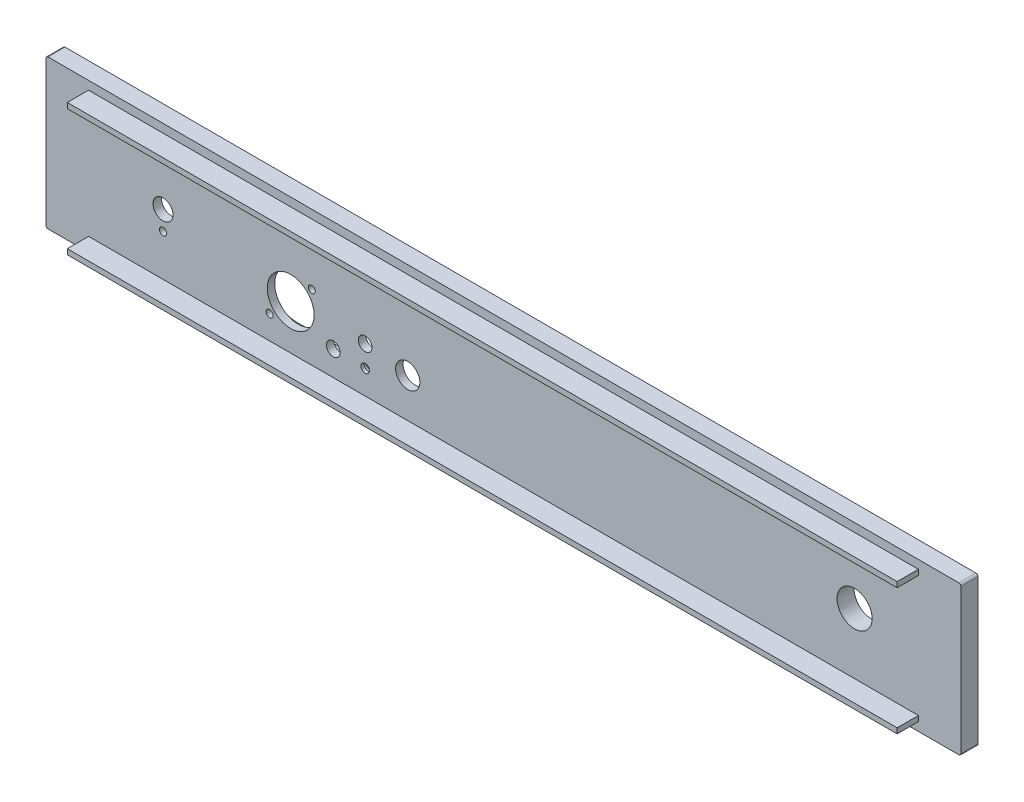
SolidWorks part; units mm, degrees
ref_plane "前基準面" through (0, 0, 0) normal (0, 0, 1) x (1, 0, 0)
ref_plane "上基準面" through (0, 0, 0) normal (0, 1, 0) x (1, 0, 0)
ref_plane "右基準面" through (0, 0, 0) normal (1, 0, 0) x (0, 0, -1)
sketch "草圖1" plane through (0, 0, 0) normal (0, 0, 1) x (1, 0, 0)
  line L1 (-215, -35) -> (215, -35)
  line L2 (-215, -35) -> (-215, 35)
  line L3 (-215, 35) -> (215, 35)
  line L4 (215, -35) -> (215, 35)
  line L5 (-215, -35) -> (215, 35) construction
  line L6 (-215, 35) -> (215, -35) construction
  point P0 (0, 0)
  dimension "D1" = 70
  dimension "D2" = 430
extrude "填料-伸長1" add sketch "草圖1" along normal blind 8
fillet "圓角1" radius 1 4 edges at (-215, 35, 4) (-215, -35, 4) (215, -35, 4) (215, 35, 4)
sketch "草圖2" plane through (0, 0, 8) normal (0, 0, 1) x (1, 0, 0)
  line L0 (214, 35) -> (-214, 35) construction
  line L1 (-195, 31) -> (195, 31)
  line L2 (-195, 31) -> (-195, 28.5)
  line L3 (-195, 28.5) -> (195, 28.5)
  line L4 (195, 31) -> (195, 28.5)
  line L5 (195, -28.5) -> (-195, -28.5)
  line L6 (195, -28.5) -> (195, -31)
  line L7 (195, -31) -> (-195, -31)
  line L8 (-195, -28.5) -> (-195, -31)
  line L9 (-215, 34) -> (-215, -34) construction
  line L11 (215, -34) -> (215, 34) construction
  dimension "D1" = 4
  dimension "D2" = 62
  dimension "D3" = 2.5
  dimension "D4" = 2.5
  dimension "D5" = 20
  dimension "D6" = 20
  dimension "D7" = 20
extrude "填料-伸長2" add sketch "草圖2" along normal blind 10
sketch "草圖3" plane through (0, 0, 0) normal (0, 0, -1) x (-1, 0, 0)
  line L0 (215, 0) -> (-215, 0)
  line L1 (215, 34) -> (215, -34) construction
  line L2 (-215, -34) -> (-215, 34) construction
  line L3 (115, -20) -> (35, -20)
  line L5 (214, -35) -> (-214, -35) construction
  circle A0 centre (-180.2944, 0) radius 8.6085
  circle A1 centre (100, -7.5) radius 11
  circle A2 centre (90.1, 2.4) radius 1.65
  circle A3 centre (109.9, -17.4) radius 1.65
  circle A4 centre (80, -16.75) radius 3.25
  circle A5 centre (65, -17.2) radius 2
  circle A6 centre (45, -10.11) radius 5.7
  circle A7 centre (160, 0) radius 4.7
  circle A8 centre (160, -9) radius 1.7
  circle A9 centre (65, -7.2) radius 3.2
  dimension "D2" = 4
  dimension "D4" = 22
  dimension "D9" = 3.3
  dimension "D10" = 3.3
  dimension "D15" = 6.5
  dimension "D16" = 11.4
  dimension "D22" = 9.4
  dimension "D24" = 3.4
  dimension "D26" = 6.4
  dimension "D1" = 12.5
  dimension "D3" = 2.8
  dimension "D5" = 19.8
  dimension "D6" = 19.8
  dimension "D7" = 9.9
  dimension "D8" = 9.9
  dimension "D11" = 20
  dimension "D12" = 15
  dimension "D13" = 20
  dimension "D14" = 3.25
  dimension "D17" = 9.89
  dimension "D18" = 10
  dimension "D19" = 15
  dimension "D20" = 100
  dimension "D21" = 15
  dimension "D23" = 9
  dimension "D25" = 60
  dimension "D27" = 20
  dimension "D28" = 10
extrude "除料-伸長1" cut sketch "草圖3" against normal through all contours A2 | L0 A1 | L0 A1 | A3 | A4 | A6 | A7 | A8 | L0 A7 | A5 | A9
sketch "草圖4" plane through (0, 0, 0) normal (0, 0, -1) x (-1, 0, 0)
  line L0 (45, -7.5) -> (105, -7.5) construction
  line L1 (45, 7.5) -> (105, 7.5)
  line L2 (45, -22.5) -> (105, -22.5)
  line L3 (214, -35) -> (-214, -35) construction
  line L4 (215, 34) -> (215, -34) construction
  arc A0 (45, 7.5) -> (45, -22.5) centre (45, -7.5) ccw
  arc A1 (105, -22.5) -> (105, 7.5) centre (105, -7.5) ccw
  point P2 (75, -7.5)
  dimension "D1" = 15
  dimension "D2" = 60
  dimension "D3" = 27.5
  dimension "D4" = 140
extrude "除料-伸長2" cut sketch "草圖4" against normal blind 4.5
sketch "草圖5" plane through (0, 0, 4.5) normal (0, 0, -1) x (-1, 0, 0)
  circle A0 centre (65, -17.2) radius 3.5
  dimension "D1" = 7
extrude "除料-伸長3" cut sketch "草圖5" against normal blind 2
sketch "草圖6" plane through (0, 0, 0) normal (0, 0, -1) x (-1, 0, 0)
  line L0 (214, -35) -> (-214, -35) construction
  line L1 (-215, -34) -> (-215, 34) construction
  circle A0 centre (-165, 0) radius 8.25
  dimension "D1" = 16.5
  dimension "D2" = 35
  dimension "D3" = 50
extrude "除料-伸長4" cut sketch "草圖6" against normal through all
sketch "草圖7" plane through (0, 0, 0) normal (0, 0, -1) x (-1, 0, 0)
  circle A0 centre (160, 0.6094) radius 20
  dimension "D1" = 40
extrude "除料-伸長5" cut sketch "草圖7" against normal blind 4
